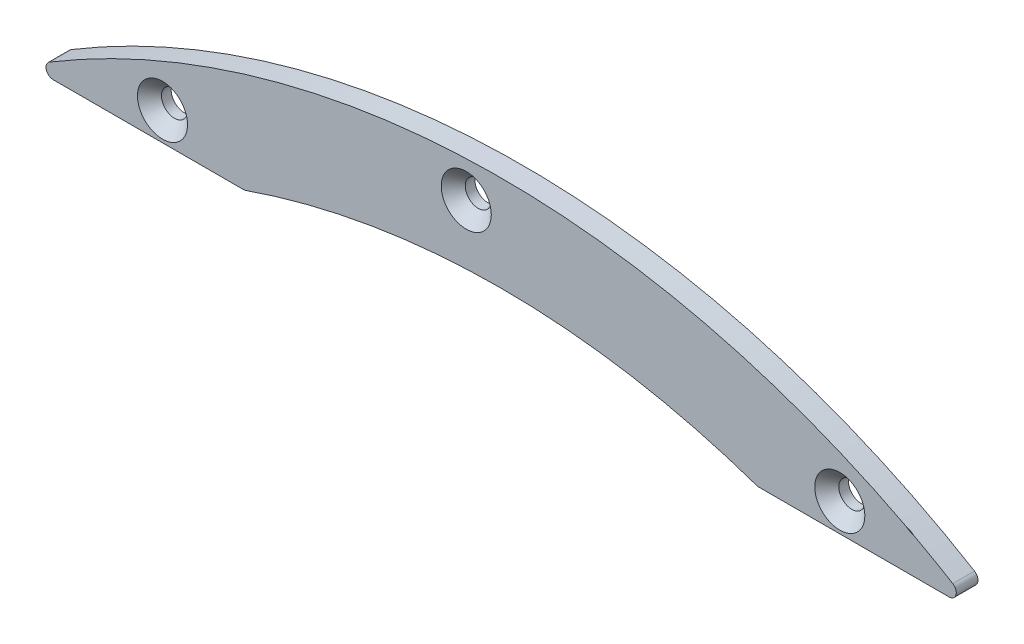
SolidWorks part; units mm, degrees
material "Alu 5754 (AG3)"
ref_plane "Face" through (0, 0, 0) normal (0, 0, 1) x (1, 0, 0)
ref_plane "Dessus" through (0, 0, 0) normal (0, 1, 0) x (1, 0, 0)
ref_plane "Droite" through (0, 0, 0) normal (1, 0, 0) x (0, 0, -1)
sketch "Esquisse1" plane through (0, 0, 0) normal (0, 0, 1) x (1, 0, 0)
  line L0 (-154.75, 254.46) -> (-88.6499, 254.46)
  line L1 (88.6499, 254.46) -> (154.75, 254.46)
  line L2 (-88.6499, 254.46) -> (88.6499, 254.46) construction
  line L3 (0, 254.46) -> (0, 269.46) construction
  line L4 (-157.25, 256.96) -> (-157.25, 79.5905) construction
  line L5 (157.25, 256.96) -> (157.25, 82.8346) construction
  arc A0 (156.0398, 259.1016) -> (-156.0398, 259.1016) centre (0, 0) ccw
  arc A1 (88.6499, 254.46) -> (-88.6499, 254.46) centre (0, 0) ccw
  arc A2 (156.0398, 259.1016) -> (154.75, 254.46) centre (154.75, 256.96) cw
  arc A3 (-156.0398, 259.1016) -> (-154.75, 254.46) centre (-154.75, 256.96) ccw
  dimension "D1" = 33
  dimension "D3" = 2.5
  dimension "D2" = 15
  dimension "D4" = 314.5
extrude "Boss.-Extru.1" add sketch "Esquisse1" along normal mid plane 7.5
hole_wizard "Fraisage pour vis à tête fraisée M81" positions "Esquisse3" profile "Esquisse2" countersink size "M8" standard "ISO" end condition through all
sketch "Esquisse3" plane through (0, 0, 3.75) normal (0, 0, 1) x (1, 0, 0)
  line L0 (-117, 264.2137) -> (117, 264.2137) construction
  line L1 (-117, 264.2137) -> (-122.4662, 276.5576) construction
  line L3 (0, 264.2137) -> (0, 0) construction
  arc A4 (156.0398, 259.1016) -> (-156.0398, 259.1016) centre (0, 0) ccw construction
  point P0 (-12.0579, 289.7317)
  point P2 (117, 264.2137)
  point P4 (-117, 264.2137)
  point P44 (145.25, 274.9597)
  dimension "D3" = 13.5
  dimension "D1" = 158
  dimension "D2" = 234
  dimension "D4" = 108
  dimension "D5" = 10.746
  dimension "D6" = 28.25
sketch "Esquisse2" plane through (-12.0579, 289.7317, 3.75) normal (1, 0, 0) x (0, -1, 0)
  line L0 (0, 0) -> (0, 7.5)
  line L1 (0, 7.5) -> (4.5, 7.5)
  line L2 (4.5, 7.5) -> (4.5, 4.15)
  line L3 (4.5, 4.15) -> (8.65, 0)
  line L5 (8.65, 0) -> (0, 0)
  line L6 (-4.5, 4.15) -> (-8.65, 0) construction
  line L11 (0, -6.35) -> (0, 107.95) construction
  dimension "Diamètre du perçage jusqu'au prochain" = 9
  dimension "Profondeur du perçage jusqu'au prochain" = 7.5
  dimension "Diamètre du fraisage entrant" = 17.3
  dimension "Angle du fraisage entrant" = 90
sketch "Esquisse4" plane through (0, 0, -3.75) normal (0, 0, -1) x (-1, 0, 0)
  line L0 (25.4204, 281.7488) -> (36.7341, 293.0625)
  line L1 (40.2697, 289.5269) -> (44.5123, 285.2843)
  line L2 (48.0478, 281.7488) -> (36.7341, 270.4351)
  line L3 (33.1986, 273.9706) -> (28.956, 278.2132)
  line L4 (34.6449, 267.2236) -> (34.9664, 269.7028) construction
  line L5 (15.8405, 287.294) -> (25.0868, 281.3353) construction
  line L6 (-3.4566, 287.7239) -> (-3.4566, 267.4908) construction
  arc A0 (36.7341, 293.0625) -> (40.2697, 289.5269) centre (38.5019, 291.2947) cw
  arc A1 (44.5123, 285.2843) -> (48.0478, 281.7488) centre (46.2801, 283.5165) cw
  arc A2 (36.7341, 270.4351) -> (33.1986, 273.9706) centre (34.9664, 272.2028) cw
  arc A3 (28.956, 278.2132) -> (25.4204, 281.7488) centre (27.1882, 279.981) cw
  arc A4 (88.6499, 254.46) -> (-88.6499, 254.46) centre (0, 0) ccw construction
  circle A6 centre (12.0579, 289.7317) radius 4.5 construction
  point P22 (12.0579, 289.7317)
  dimension "D1" = 2.5
  dimension "D2" = 16
  dimension "D3" = 16
  dimension "D4" = 2.5
  dimension "D5" = 11
  dimension "D6" = 45
extrude "Enlèv. mat.-Extru.1" cut sketch "Esquisse4" against normal blind 3
